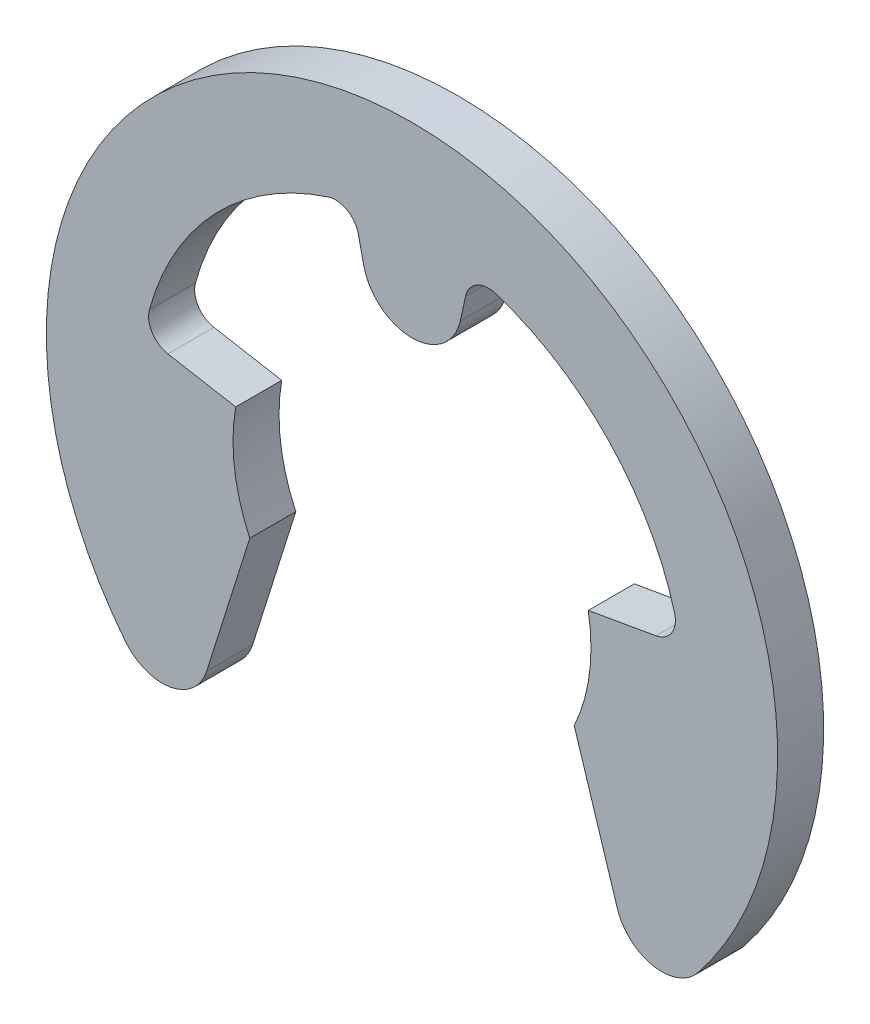
SolidWorks part; units mm, degrees
ref_plane "Plane1" through (0, 0, 0) normal (0, 0, 1) x (1, 0, 0)
ref_plane "Plane2" through (0, 0, 0) normal (0, 1, 0) x (1, 0, 0)
ref_plane "Plane3" through (0, 0, 0) normal (1, 0, 0) x (0, 0, -1)
sketch "BodySke" plane through (0, 0, 0) normal (0, 0, 1) x (1, 0, 0)
  line L0 (-0.7581, 0) -> (0.7581, 0) construction
  line L1 (0, 0) -> (0, 7.15) construction
  line L2 (0, 0) -> (0.1641, 0.7402) construction
  line L3 (0, 0) -> (6.4801, -3.0217) construction
  line L4 (0, 0) -> (-0.1641, 0.7402) construction
  line L5 (0, 0) -> (-6.4801, -3.0217) construction
  line L6 (3.4468, 0.6078) -> (4.7737, 0.8417)
  line L7 (-3.4468, 0.6078) -> (-4.7737, 0.8417)
  line L8 (0, 0) -> (7.0414, 1.2416) construction
  line L9 (3.1721, -1.4792) -> (4.015, -4.1526)
  line L10 (-3.1721, -1.4792) -> (-4.015, -4.1526)
  line L11 (0.9439, 4.2575) -> (1.0492, 4.7324)
  line L12 (-0.9439, 4.2575) -> (-1.0492, 4.7324)
  line L13 (0, 0) -> (-7.0414, 1.2416) construction
  circle A0 centre (0, 0) radius 3.5 construction
  arc A1 (5.1344, 1.412) -> (1.6346, 5.0679) centre (0, 0) ccw
  arc A2 (5.6, -4.4456) -> (-5.6, -4.4456) centre (0, 0) ccw
  arc A3 (3.1721, -1.4792) -> (3.4468, 0.6078) centre (0, 0) ccw
  arc A4 (-1.6346, 5.0679) -> (-5.1344, 1.412) centre (0, 0) ccw
  arc A5 (4.7737, 0.8417) -> (5.1344, 1.412) centre (4.6945, 1.291) ccw
  arc A7 (1.6346, 5.0679) -> (1.0492, 4.7324) centre (1.4946, 4.6337) ccw
  arc A8 (-3.4468, 0.6078) -> (-3.1721, -1.4792) centre (0, 0) ccw
  arc A9 (-5.1344, 1.412) -> (-4.7737, 0.8417) centre (-4.6945, 1.291) ccw
  arc A10 (-0.9439, 4.2575) -> (0.9439, 4.2575) centre (0, 4.4668) ccw
  arc A11 (-1.0492, 4.7324) -> (-1.6346, 5.0679) centre (-1.4946, 4.6337) ccw
  arc A12 (-5.6, -4.4456) -> (-4.015, -4.1526) centre (-4.8853, -3.8782) ccw
  arc A13 (4.015, -4.1526) -> (5.6, -4.4456) centre (4.8853, -3.8782) ccw
  dimension "D1" = 35
  dimension "GrooveDia" = 7
  dimension "OutsideDia" = 14.3
  dimension "D3" = 25
  dimension "TipRad" = 0.9125
  dimension "D2" = 160
  dimension "CavityDia" = 10.65
  dimension "CavityFilletRad" = 0.4563
  dimension "D4" = 35
extrude "Body" add sketch "BodySke" against normal blind 0.9
equation "' \"Thickness@Body\" = 0.2"
equation "' \"GrooveDia@BodySke\" = 0.8"
equation "' \"OutsideDia@BodySke\" = 2.25"
equation "' \"Thickness@Body\" = 2.5"
equation "' \"GrooveDia@BodySke\" = 30"
equation "' \"OutsideDia@BodySke\" = 52.6"
equation "\"CavityDia@BodySke\" = (\"OutsideDia@BodySke\"  + \"GrooveDia@BodySke\") / 2 "
equation "\"CavityFilletRad@BodySke\" =  (\"CavityDia@BodySke\" - \"GrooveDia@BodySke\") / 2 * 0.25"
equation "\"TipRad@BodySke\" = (\"OutsideDia@BodySke\"  - \"GrooveDia@BodySke\") / 2 * 0.25"
